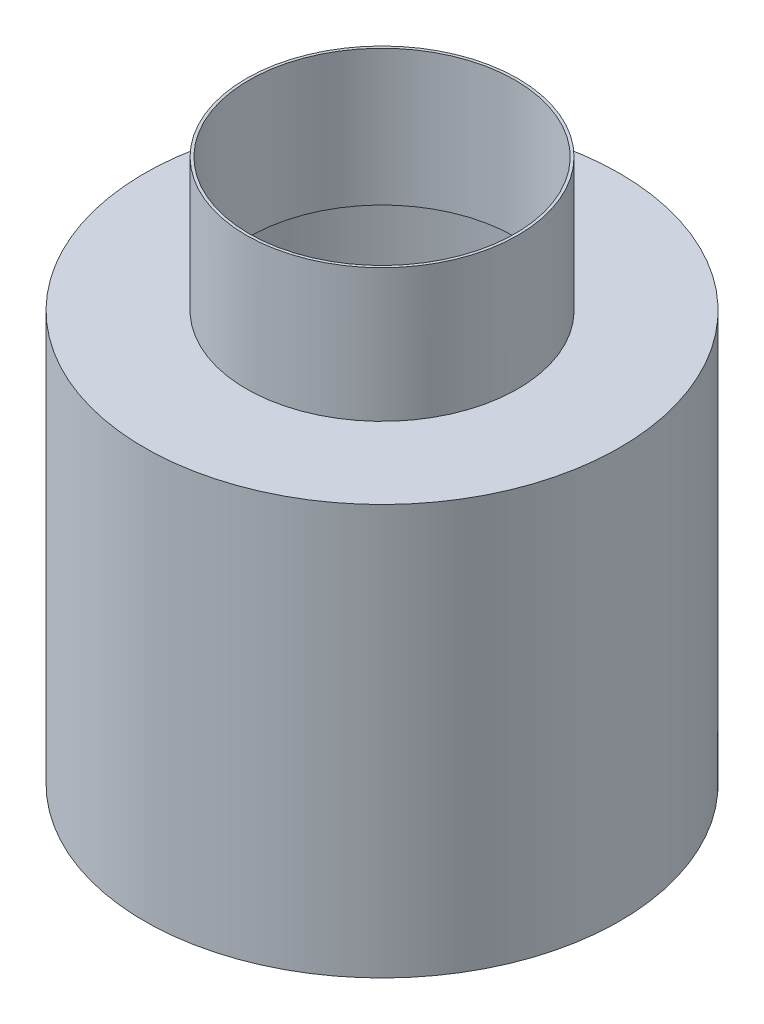
SolidWorks part; units mm, degrees
ref_plane "Front Plane" through (0, 0, 0) normal (0, 0, 1) x (1, 0, 0)
ref_plane "Top Plane" through (0, 0, 0) normal (0, 1, 0) x (1, 0, 0)
ref_plane "Right Plane" through (0, 0, 0) normal (1, 0, 0) x (0, 0, -1)
sketch "Sketch1" plane through (0, 0, 0) normal (0, 1, 0) x (1, 0, 0)
  circle A0 centre (0, 0) radius 100
  dimension "D1" = 200
extrude "Boss-Extrude1" add sketch "Sketch1" along normal blind 98
sketch "Sketch3" plane through (0, 98, 0) normal (0, 1, 0) x (1, 0, 0)
  circle A0 centre (0, 0) radius 98
  dimension "D1" = 196
extrude "Cut-Extrude2" cut sketch "Sketch3" against normal blind 397
sketch "Sketch5" plane through (0, 0, 0) normal (0, -1, 0) x (1, 0, 0)
  circle A0 centre (0, 0) radius 175
  circle A1 centre (0, 0) radius 98
  dimension "D1" = 350
extrude "Boss-Extrude2" add sketch "Sketch5" along normal blind 2
sketch "Sketch7" plane through (0, -2, 0) normal (0, -1, 0) x (1, 0, 0)
  circle A0 centre (0, 0) radius 175
  circle A1 centre (0, 0) radius 173
  circle A2 centre (0, 0) radius 175 construction
  dimension "D1" = 2
extrude "Boss-Extrude3" add sketch "Sketch7" along normal blind 300
sketch "Sketch8" plane through (0, -302, 0) normal (0, -1, 0) x (1, 0, 0)
  circle A0 centre (0, 0) radius 175
  dimension "D1" = 350
extrude "Boss-Extrude4" add sketch "Sketch8" against normal blind 2
